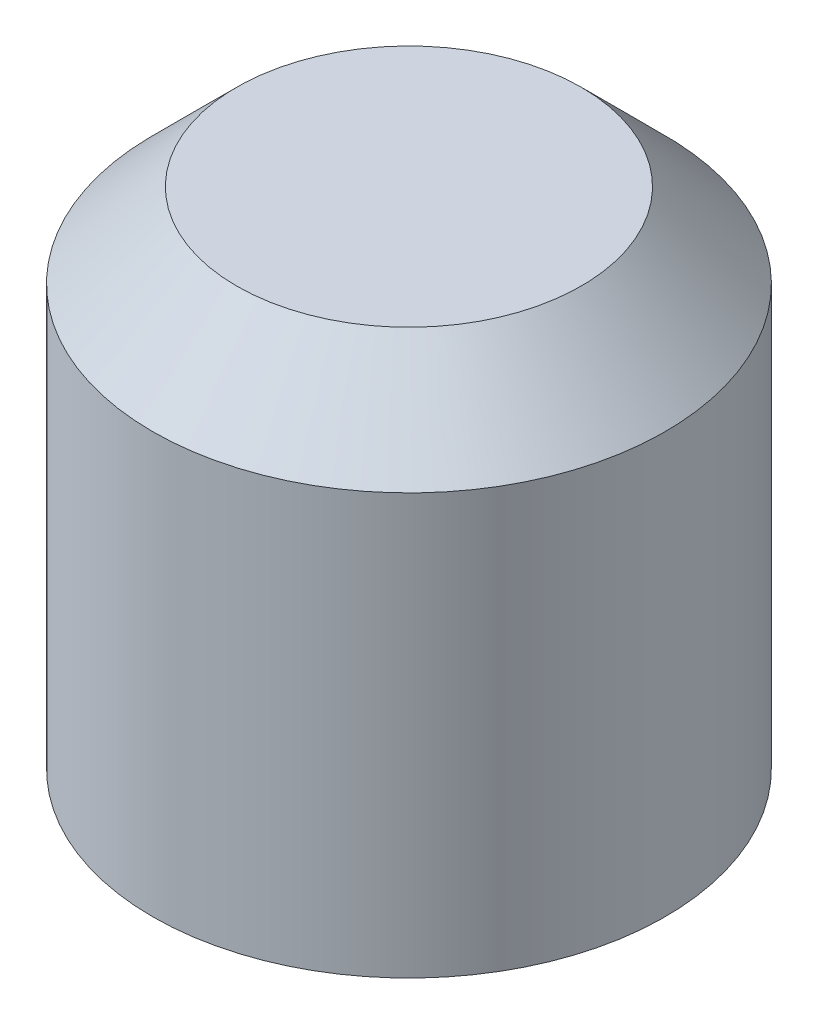
SolidWorks part; units mm, degrees
ref_plane "Front Plane" through (0, 0, 0) normal (0, 0, 1) x (1, 0, 0)
ref_plane "Top Plane" through (0, 0, 0) normal (0, 1, 0) x (1, 0, 0)
ref_plane "Right Plane" through (0, 0, 0) normal (1, 0, 0) x (0, 0, -1)
sketch "Sketch2" plane through (0, 0, 0) normal (0, 1, 0) x (1, 0, 0)
  circle A0 centre (0, 0) radius 1.525
  dimension "D1" = 3.05
extrude "Boss-Extrude1" add sketch "Sketch2" along normal blind 3
chamfer "Chamfer1" distance 0.5 angle 45 1 edges at (0, 3, 1.525)
